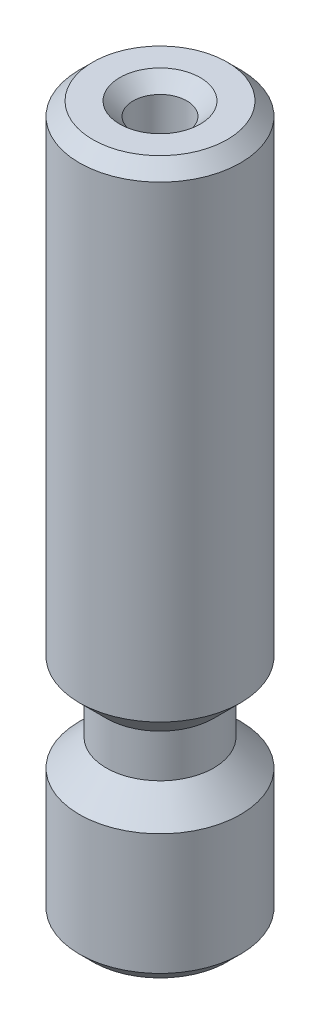
SolidWorks part; units mm, degrees
material "AISI 304"
ref_plane "Front Plane" through (0, 0, 0) normal (0, 0, 1) x (1, 0, 0)
ref_plane "Top Plane" through (0, 0, 0) normal (0, 1, 0) x (1, 0, 0)
ref_plane "Right Plane" through (0, 0, 0) normal (1, 0, 0) x (0, 0, -1)
sketch "Sketch4" plane through (0, 0, 0) normal (0, 0, 1) x (1, 0, 0)
  line L0 (0, -1000) -> (0, 49000) construction
  line L1 (-1, 0) -> (-1, 26.5)
  line L2 (-2, 6) -> (-2, 7.6)
  line L3 (-3, 0) -> (-3, 5)
  line L4 (-3, 0) -> (-1, 0)
  line L5 (-1, 26.5) -> (-3, 26.5)
  line L6 (-3, 5) -> (-2, 6)
  line L7 (0, 0) -> (-11.9274, 0) construction
  line L8 (-3, 8.6) -> (-3, 26.5)
  line L9 (-3, 8.6) -> (-2, 7.6)
  dimension "D2" = 1
  dimension "D3" = 3
  dimension "D4" = 5
  dimension "D5" = 45
  dimension "D6" = 26.5
  dimension "D7" = 45
  dimension "D8" = 3
  dimension "D9" = 1
  dimension "D10" = 8.6
revolve "Revolve1" add sketch "Sketch4" angle 360 about L0
chamfer "Chamfer2" distance 0.5 angle 45 3 edges at (1, 26.5, 0) (3, 0, 0) (3, 26.5, 0)
